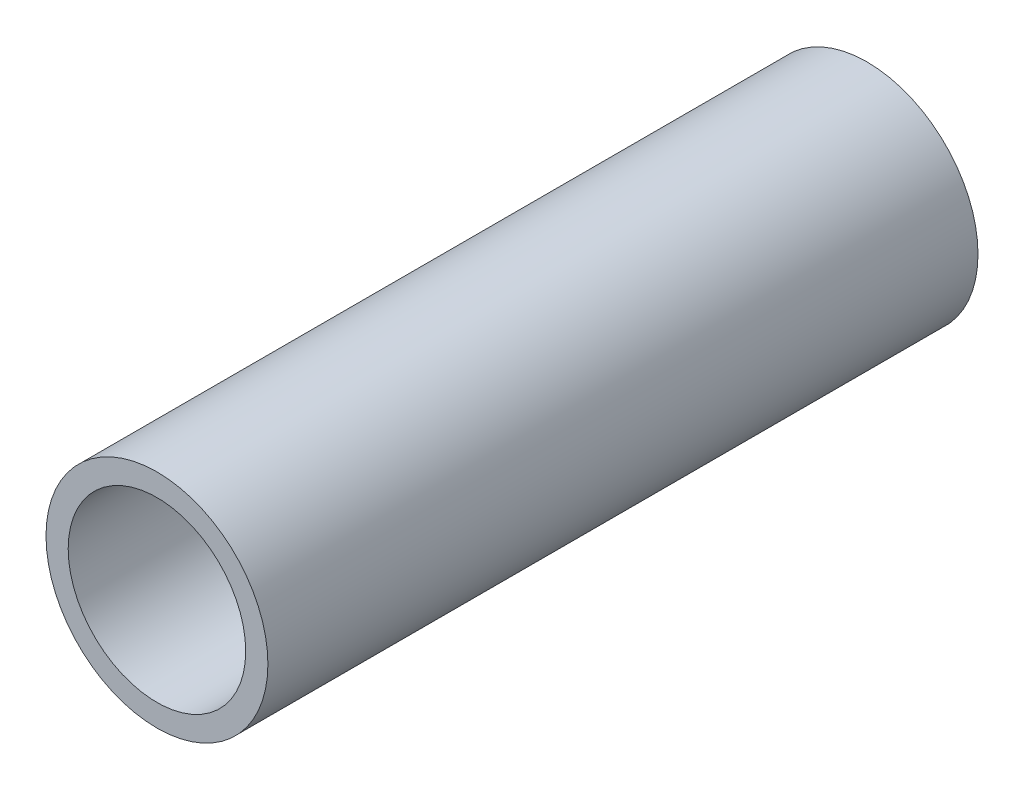
SolidWorks part; units mm, degrees
ref_plane "Front Plane" through (0, 0, 0) normal (0, 0, 1) x (1, 0, 0)
ref_plane "Top Plane" through (0, 0, 0) normal (0, 1, 0) x (1, 0, 0)
ref_plane "Right Plane" through (0, 0, 0) normal (1, 0, 0) x (0, 0, -1)
sketch "Sketch1" plane through (0, 0, 0) normal (0, 0, 1) x (1, 0, 0)
  circle A0 centre (0, 0) radius 1
  circle A1 centre (0, 0) radius 1.25
  dimension "D1" = 2
  dimension "D2" = 2.5
extrude "Boss-Extrude1" add sketch "Sketch1" along normal blind 8
